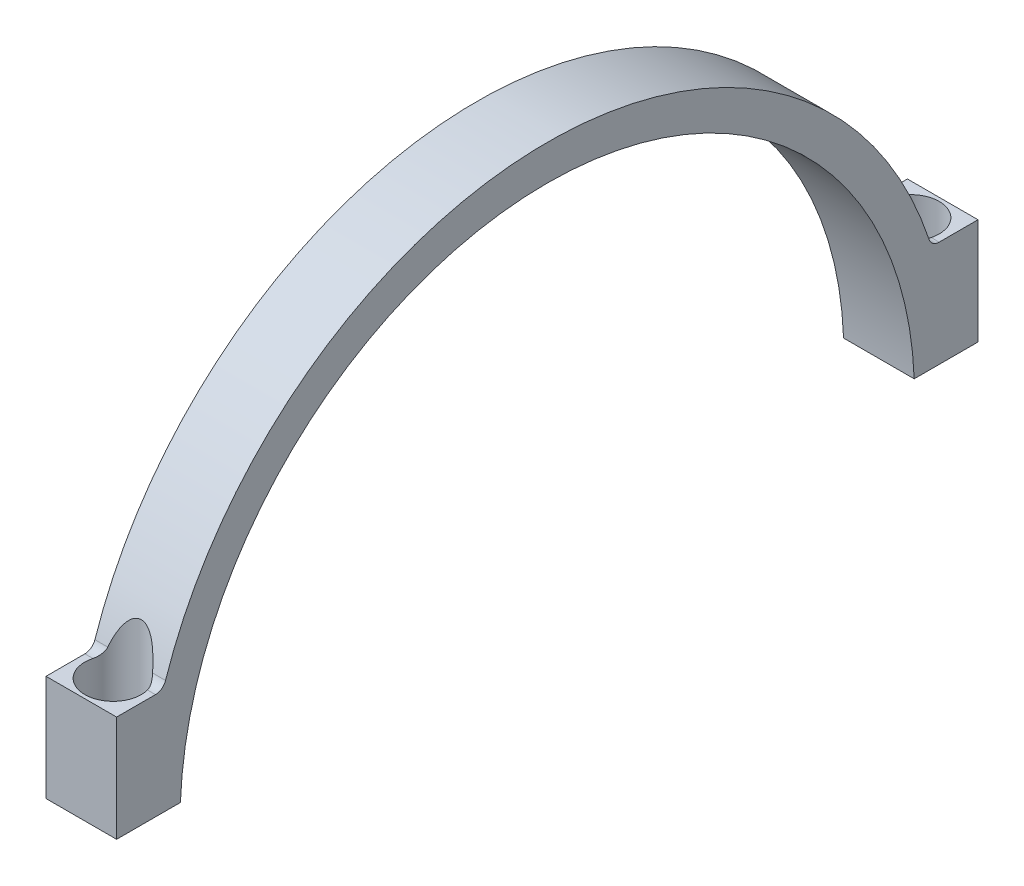
SolidWorks part; units mm, degrees
material "1060 Alloy"
ref_plane "Front Plane" through (0, 0, 0) normal (0, 0, 1) x (1, 0, 0)
ref_plane "Top Plane" through (0, 0, 0) normal (0, 1, 0) x (1, 0, 0)
ref_plane "Right Plane" through (0, 0, 0) normal (1, 0, 0) x (0, 0, -1)
sketch "Sketch1" plane through (0, 0, 0) normal (1, 0, 0) x (0, 0, -1)
  line L2 (-61.0015, 2) -> (-51.9615, 2)
  line L3 (51.9615, 2) -> (60.9985, 2)
  line L4 (-61.0015, 2) -> (-61.0015, 17)
  line L5 (-61.0015, 17) -> (-55.4977, 17)
  line L6 (60.9985, 2) -> (60.9985, 17)
  line L7 (60.9985, 17) -> (55.4977, 17)
  arc A0 (51.9615, 2) -> (-51.9615, 2) centre (0, 0) ccw
  arc A1 (54.0747, 18.0256) -> (-54.0747, 18.0256) centre (0, 0) ccw
  circle A2 centre (0, 0) radius 57 construction
  circle A3 centre (0, 0) radius 52 construction
  arc A5 (55.4977, 17) -> (54.0747, 18.0256) centre (55.4977, 18.5) cw
  arc A7 (-55.4977, 17) -> (-54.0747, 18.0256) centre (-55.4977, 18.5) ccw
  dimension "D1" = 104
  dimension "D2" = 122
  dimension "D3" = 9.04
  dimension "D4" = 9.037
  dimension "D5" = 5
extrude "Boss-Extrude1" add sketch "Sketch1" along normal blind 10
hole_wizard "M4 Tapped Hole1" positions "Sketch5" profile "Sketch4" tap size "M4" standard "ISO"
sketch "Sketch5" plane through (0, 17, 0) normal (0, 1, 0) x (1, 0, 0)
  line L0 (10, 60.9985) -> (10, 55.4977) construction
  line L1 (10, -61.0015) -> (0, -61.0015) construction
  line L2 (10, 60.9985) -> (0, 60.9985) construction
  line L4 (10, -55.4977) -> (10, -61.0015) construction
  point P0 (5, 56.4985)
  point P11 (5, -56.5015)
  dimension "D1" = 5
  dimension "D2" = 4.5
  dimension "D3" = 4.5
  dimension "D4" = 5
sketch "Sketch4" plane through (5, 17, -56.4985) normal (1, 0, 0) x (0, 0, 1)
  line L0 (0, 0) -> (0, 21.0914)
  line L1 (0, 21.0914) -> (1.65, 20.1)
  line L2 (1.65, 20.1) -> (1.65, 0)
  line L5 (1.65, 0) -> (0, 0)
  line L10 (0, 21.0914) -> (-1.65, 20.1) construction
  line L11 (0, -6.35) -> (0, 107.95) construction
  dimension "Tap Drill Dia." = 3.3
  dimension "Tap Drill Depth" = 20.1
  dimension "Drill Angle" = 118
cosmetic thread "Hole Thread3" parameters "D1"=8, "D2"=4
cosmetic thread "Hole Thread4" parameters "D1"=8, "D2"=4
sketch "Sketch7" plane through (0, 17, 0) normal (0, 1, 0) x (1, 0, 0)
  circle A0 centre (5, 56.4985) radius 4
  circle A1 centre (5, -56.5015) radius 4
  dimension "D1" = 8
extrude "Cut-Extrude1" cut sketch "Sketch7" against normal blind 6.6 and the other way blind 10
